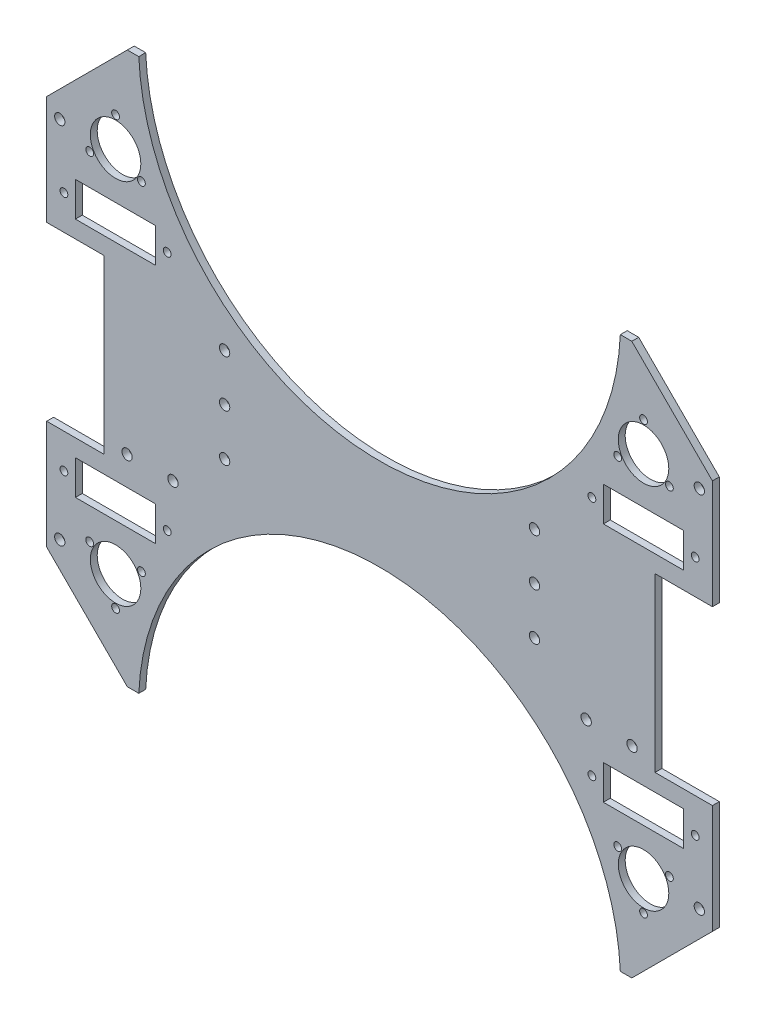
SolidWorks part; units mm, degrees
ref_plane "Plan de face" through (0, 0, 0) normal (0, 0, 1) x (1, 0, 0)
ref_plane "Plan de dessus" through (0, 0, 0) normal (0, 1, 0) x (1, 0, 0)
ref_plane "Plan de droite" through (0, 0, 0) normal (1, 0, 0) x (0, 0, -1)
sketch "Esquisse1" plane through (0, 0, 0) normal (0, 0, 1) x (1, 0, 0)
  line L0 (-145, 85) -> (-109.8862, 120.1138)
  line L1 (-109.8862, 120.1138) -> (-105, 125) construction
  line L2 (109.8862, 120.1138) -> (145, 85)
  line L3 (-85, 145) -> (85, 145) construction
  line L4 (105, -125) -> (109.8862, -120.1138) construction
  line L5 (-145, -145) -> (145, 145) construction
  line L6 (-145, 145) -> (145, -145) construction
  line L7 (85, 145) -> (105, 125) construction
  line L8 (-105, -125) -> (-85, -145) construction
  line L9 (-105, -125) -> (105, -125) construction
  line L10 (-105, 125) -> (105, 125) construction
  line L11 (85, -145) -> (105, -125) construction
  line L12 (-105, 125) -> (-85, 145) construction
  line L13 (105, 125) -> (109.8862, 120.1138) construction
  line L14 (-85, -145) -> (85, -145) construction
  line L15 (-109.8862, -120.1138) -> (-105, -125) construction
  line L16 (-109.8862, 120.1138) -> (-104.8862, 120.1138)
  line L17 (104.8862, 120.1138) -> (109.8862, 120.1138)
  line L18 (-145, 0) -> (145, 0) construction
  line L19 (145, -37.5) -> (145, -85)
  line L20 (104.8862, -120.1138) -> (109.8862, -120.1138)
  line L21 (-109.8862, -120.1138) -> (-104.8862, -120.1138)
  line L22 (-145, 85) -> (-145, 37.5)
  line L23 (145, -37.5) -> (120, -37.5)
  line L24 (109.8862, -120.1138) -> (145, -85)
  line L25 (-145, -85) -> (-109.8862, -120.1138)
  line L26 (-145, -37.5) -> (-145, -85)
  line L27 (-145, 37.5) -> (-120, 37.5)
  line L28 (0, 125) -> (0, -125) construction
  line L29 (-145, -37.5) -> (-120, -37.5)
  line L30 (-120, 37.5) -> (-120, -37.5)
  line L31 (120, 37.5) -> (120, -37.5)
  line L32 (145, 37.5) -> (120, 37.5)
  line L33 (145, 85) -> (145, 37.5)
  arc A0 (-104.8862, 120.1138) -> (104.8862, 120.1138) centre (0, 125) ccw
  arc A1 (-104.8862, -120.1138) -> (104.8862, -120.1138) centre (0, -125) cw
  point P0 (0, 0)
  point P30 (-145, 0)
  dimension "D3" = 105
  dimension "D4" = 85
  dimension "D8" = 250
  dimension "D1" = 290
  dimension "D2" = 290
  dimension "D6" = 60
  dimension "D7" = 60
  dimension "D11" = 25
  dimension "D5" = 5
  dimension "D10" = 5
  dimension "D12" = 37.5
  dimension "D9" = 75
  dimension "D13" = 47.5
extrude "Boss.-Extru.1" add sketch "Esquisse1" along normal blind 3
sketch "Esquisse4" plane through (0, 0, 3) normal (0, 0, 1) x (1, 0, 0)
  line L1 (-145, 85) -> (-133.6, 85) construction
  line L2 (-145, 85) -> (-145, 73.6) construction
  line L3 (-145, 73.6) -> (-133.6, 73.6) construction
  line L4 (-133.6, 85) -> (-133.6, 73.6) construction
  line L5 (-145, -85) -> (-133.6, -85) construction
  line L6 (-145, -85) -> (-145, -73.6) construction
  line L7 (-145, -73.6) -> (-133.6, -73.6) construction
  line L8 (-133.6, -85) -> (-133.6, -73.6) construction
  line L9 (145, 85) -> (133.6, 85) construction
  line L10 (145, 85) -> (145, 73.6) construction
  line L11 (145, 73.6) -> (133.6, 73.6) construction
  line L12 (133.6, 85) -> (133.6, 73.6) construction
  line L13 (145, -85) -> (133.6, -85) construction
  line L14 (145, -85) -> (145, -73.6) construction
  line L15 (145, -73.6) -> (133.6, -73.6) construction
  line L16 (133.6, -85) -> (133.6, -73.6) construction
  point P20 (-139.3, 79.3)
  point P21 (139.3, 79.3)
  point P22 (-139.3, -79.3)
  point P23 (139.3, -79.3)
  dimension "D1" = 11.4
  dimension "D2" = 11.4
  dimension "D3" = 11.4
  dimension "D4" = 11.4
  dimension "D5" = 11.4
  dimension "D6" = 11.4
  dimension "D7" = 11.4
  dimension "D8" = 11.4
  dimension "D9" = 5.7
  dimension "D10" = 5.7
  dimension "D11" = 5.7
  dimension "D12" = 5.7
  dimension "D13" = 5.7
  dimension "D14" = 5.7
  dimension "D15" = 5.7
  dimension "D16" = 5.7
hole_wizard "Dégagement M41" positions "Esquisse3D1" profile "Esquisse7" hole size "M4" standard "ISO"
sketch3d "Esquisse3D1"
  point P0 (-139.3, 79.3, 3)
  point P3 (139.3, 79.3, 3)
  point P6 (139.3, -79.3, 3)
  point P9 (-139.3, -79.3, 3)
sketch "Esquisse7" plane through (-139.3, 79.3, 3) normal (1, 0, 0) x (0, -1, 0)
  line L0 (0, 0) -> (0, 11.3519)
  line L1 (0, 11.3519) -> (2.25, 10)
  line L2 (2.25, 10) -> (2.25, 0)
  line L5 (2.25, 0) -> (0, 0)
  line L10 (0, 11.3519) -> (-2.25, 10) construction
  line L11 (0, -6.35) -> (0, 107.95) construction
  dimension "Diamètre du perçage" = 4.5
  dimension "Profondeur du perçage" = 10
  dimension "Angle de pointe" = 118
sketch "Esquisse9" plane through (0, 0, 3) normal (0, 0, 1) x (1, 0, 0)
  line L0 (-145, 85) -> (-145, 37.5) construction
  line L1 (-104.8862, 120.1138) -> (-109.8862, 120.1138) construction
  line L2 (0, 0) -> (-151.8915, 0) construction
  line L3 (0, 0) -> (0, 118.8596) construction
  circle A0 centre (-115, 80.1138) radius 15 construction
  circle A1 centre (-115, -80.1138) radius 15 construction
  circle A2 centre (115, -80.1138) radius 15 construction
  circle A3 centre (115, 80.1138) radius 15 construction
  point P4 (-107.3862, 120.1138)
  dimension "D1" = 30
  dimension "D2" = 30
  dimension "D3" = 40
hole_wizard "Dégagement M201" positions "Esquisse3D2" profile "Esquisse13" hole size "M20" standard "ISO"
sketch3d "Esquisse3D2"
  point P0 (-115, 80.1138, 3)
  point P3 (115, 80.1138, 3)
  point P6 (115, -80.1138, 3)
  point P9 (-115, -80.1138, 3)
sketch "Esquisse13" plane through (-115, 80.1138, 3) normal (1, 0, 0) x (0, -1, 0)
  line L0 (0, 0) -> (0, 16.6095)
  line L1 (0, 16.6095) -> (11, 10)
  line L2 (11, 10) -> (11, 0)
  line L5 (11, 0) -> (0, 0)
  line L10 (0, 16.6095) -> (-11, 10) construction
  line L11 (0, -6.35) -> (0, 107.95) construction
  dimension "Diamètre du perçage" = 22
  dimension "Profondeur du perçage" = 10
  dimension "Angle de pointe" = 118
sketch "Esquisse14" plane through (0, 0, 3) normal (0, 0, 1) x (1, 0, 0)
  line L0 (0, 103.8188) -> (0.0001, 103.8188) construction
  line L2 (0, -200000) -> (0, 200118.8596) construction
  line L3 (-183.8079, 0) -> (139.8999, 0) construction
  line L4 (200000, 0) -> (-200151.8915, 0) construction
  line L5 (0, 115.3562) -> (0, -78.1432) construction
  arc A0 (-115, 93.1138) -> (-103.7417, 73.6138) centre (-115, 80.1138) cw
  arc A1 (-115, 93.1138) -> (-126.2583, 73.6138) centre (-115, 80.1138) ccw
  point P15 (-103.7417, -73.6138)
  point P16 (-115, -93.1138)
  point P17 (-126.2583, -73.6138)
  point P18 (103.7417, -73.6138)
  point P19 (115, -93.1138)
  point P20 (126.2583, -73.6138)
  point P21 (103.7417, 73.6138)
  point P22 (115, 93.1138)
  point P23 (126.2583, 73.6138)
hole_wizard "Dégagement M32" positions "Esquisse20" profile "Esquisse19" hole size "M3" standard "ISO"
sketch "Esquisse20" plane through (0, 0, 3) normal (0, 0, 1) x (1, 0, 0)
  point P1 (-103.7417, 73.6138)
  point P4 (-115, 93.1138)
  point P7 (-126.2583, 73.6138)
  point P10 (-103.7417, -73.6138)
  point P13 (-126.2583, -73.6138)
  point P16 (-115, -93.1138)
  point P19 (115, -93.1138)
  point P22 (126.2583, -73.6138)
  point P25 (103.7417, -73.6138)
  point P28 (103.7417, 73.6138)
  point P31 (115, 93.1138)
  point P34 (126.2583, 73.6138)
sketch "Esquisse19" plane through (-103.7417, 73.6138, 3) normal (1, 0, 0) x (0, -1, 0)
  line L0 (0, 0) -> (0, 11.0215)
  line L1 (0, 11.0215) -> (1.7, 10)
  line L2 (1.7, 10) -> (1.7, 0)
  line L5 (1.7, 0) -> (0, 0)
  line L10 (0, 11.0215) -> (-1.7, 10) construction
  line L11 (0, -6.35) -> (0, 107.95) construction
  dimension "Diamètre du perçage" = 3.4
  dimension "Profondeur du perçage" = 10
  dimension "Angle de pointe" = 118
sketch "Esquisse21" plane through (0, 0, 3) normal (0, 0, 1) x (1, 0, 0)
  line L0 (-120, 37.5) -> (-120, -37.5) construction
  line L1 (-120, 35) -> (-80, 35) construction
  line L2 (-120, 35) -> (-120, -20) construction
  line L3 (-120, -20) -> (-80, -20) construction
  line L4 (-80, 35) -> (-80, -20) construction
  line L5 (200000, 0) -> (-200151.8915, 0) construction
  line L6 (0, 54.3754) -> (0, -32.5) construction
  line L7 (0, -200000) -> (0, 200118.8596) construction
  line L8 (120, 35) -> (120, -20) construction
  line L9 (120, 35) -> (80, 35) construction
  line L10 (80, 35) -> (80, -20) construction
  line L11 (120, -20) -> (80, -20) construction
  point P8 (-67.5, 28)
  point P9 (-67.5, -13)
  point P10 (-110, -32.5)
  point P11 (-90, -32.5)
  point P16 (-67.5, 7.5)
  point P17 (110, -32.5)
  point P18 (90, -32.5)
  point P20 (67.5, -13)
  point P21 (67.5, 7.5)
  point P22 (67.5, 28)
  dimension "D1" = 35
  dimension "D2" = 55
  dimension "D3" = 40
  dimension "D4" = 12.5
  dimension "D5" = 12.5
  dimension "D6" = 7
  dimension "D7" = 7
  dimension "D8" = 12.5
  dimension "D9" = 12.5
  dimension "D10" = 10
  dimension "D11" = 10
  dimension "D12" = 12.5
  dimension "D13" = 27.5
hole_wizard "Dégagement M43" positions "Esquisse25" profile "Esquisse26" hole size "M4" standard "ISO" end condition through all
sketch "Esquisse25" plane through (0, 0, 3) normal (0, 0, 1) x (1, 0, 0)
  point P1 (-110, -32.5)
  point P4 (-90, -32.5)
  point P7 (-67.5, -13)
  point P10 (-67.5, 7.5)
  point P13 (-67.5, 28)
  point P16 (67.5, 28)
  point P19 (67.5, 7.5)
  point P22 (67.5, -13)
  point P25 (90, -32.5)
  point P28 (110, -32.5)
sketch "Esquisse26" plane through (-110, -32.5, 3) normal (1, 0, 0) x (0, -1, 0)
  line L0 (0, 0) -> (0, 3)
  line L1 (0, 3) -> (2.25, 3)
  line L2 (2.25, 3) -> (2.25, 0)
  line L5 (2.25, 0) -> (0, 0)
  line L11 (0, -6.35) -> (0, 107.95) construction
  dimension "Diamètre du perçage jusqu'au prochain" = 4.5
  dimension "Profondeur du perçage jusqu'au prochain" = 3
sketch "Esquisse27" plane through (0, 0, 0) normal (0, 0, -1) x (-1, 0, 0)
  line L0 (-145, 37.5) -> (-145, 85) construction
  line L1 (-132.5, 60) -> (-97.5, 60)
  line L2 (-132.5, 60) -> (-132.5, 45)
  line L3 (-132.5, 45) -> (-97.5, 45)
  line L4 (-97.5, 60) -> (-97.5, 45)
  line L5 (-132.5, 60) -> (-97.5, 45) construction
  line L6 (-132.5, 45) -> (-97.5, 60) construction
  line L7 (-120, 37.5) -> (-145, 37.5) construction
  line L8 (0, 0) -> (0, 77.1679) construction
  line L9 (0, 0) -> (-86.5973, 0) construction
  line L10 (-132.5, -60) -> (-132.5, -45)
  line L11 (-132.5, -60) -> (-97.5, -45) construction
  line L12 (-132.5, -45) -> (-97.5, -45)
  line L13 (-97.5, -60) -> (-97.5, -45)
  line L14 (-132.5, -60) -> (-97.5, -60)
  line L15 (97.5, -60) -> (97.5, -45)
  line L16 (132.5, -60) -> (97.5, -60)
  line L17 (132.5, -60) -> (132.5, -45)
  line L18 (132.5, -45) -> (97.5, -45)
  line L19 (132.5, 45) -> (97.5, 45)
  line L20 (97.5, 60) -> (97.5, 45)
  line L21 (132.5, 60) -> (97.5, 60)
  line L22 (132.5, 60) -> (132.5, 45)
  point P0 (-115, 52.5)
  dimension "D1" = 30
  dimension "D2" = 35
  dimension "D3" = 15
  dimension "D4" = 15
extrude "Enlèv. mat.-Extru.2" cut sketch "Esquisse27" against normal through all
sketch "Esquisse30" plane through (0, 0, 0) normal (0, 0, -1) x (-1, 0, 0)
  line L0 (97.5, -60) -> (132.5, -60) construction
  line L1 (97.5, -45) -> (97.5, -60) construction
  line L2 (132.5, -60) -> (132.5, -45) construction
  line L3 (0, 0) -> (0, 73.3959) construction
  line L4 (0, 0) -> (-59.0579, 0) construction
  point P2 (-137.5, -52.5)
  point P4 (-92.5, -52.5)
  point P5 (92.5, 52.5)
  point P6 (92.5, -52.5)
  point P7 (137.5, -52.5)
  point P15 (137.5, 52.5)
  point P16 (-92.5, 52.5)
  point P17 (-137.5, 52.5)
  dimension "D1" = 7.5
  dimension "D2" = 7.5
  dimension "D3" = 5
  dimension "D4" = 5
hole_wizard "Dégagement M33" positions "Esquisse32" profile "Esquisse31" hole size "M3" standard "ISO"
sketch "Esquisse32" plane through (0, 0, 0) normal (0, 0, -1) x (-1, 0, 0)
  point P1 (-137.5, 52.5)
  point P4 (-92.5, 52.5)
  point P7 (-137.5, -52.5)
  point P10 (-92.5, -52.5)
  point P13 (92.5, 52.5)
  point P16 (137.5, 52.5)
  point P19 (92.5, -52.5)
  point P22 (137.5, -52.5)
sketch "Esquisse31" plane through (137.5, 52.5, 0) normal (1, 0, 0) x (0, 1, 0)
  line L0 (0, 0) -> (0, 8.0315)
  line L1 (0, 8.0315) -> (1.7, 7.01)
  line L2 (1.7, 7.01) -> (1.7, 0)
  line L5 (1.7, 0) -> (0, 0)
  line L10 (0, 8.0315) -> (-1.7, 7.01) construction
  line L11 (0, -6.35) -> (0, 107.95) construction
  dimension "Diamètre du perçage" = 3.4
  dimension "Profondeur du perçage" = 7.01
  dimension "Angle de pointe" = 118
